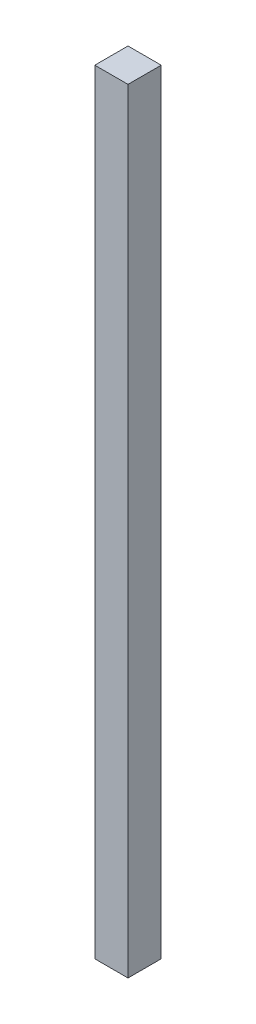
SolidWorks part; units mm, degrees
ref_plane "Plan de face" through (0, 0, 0) normal (0, 0, 1) x (1, 0, 0)
ref_plane "Plan de dessus" through (0, 0, 0) normal (0, 1, 0) x (1, 0, 0)
ref_plane "Plan de droite" through (0, 0, 0) normal (1, 0, 0) x (0, 0, -1)
sketch "Esquisse1" plane through (0, 0, 0) normal (0, 0, 1) x (1, 0, 0)
  line L1 (-41.6667, 69.6429) -> (-51.6667, 69.6429)
  line L2 (-41.6667, 69.6429) -> (-41.6667, -163.3571)
  line L3 (-41.6667, -163.3571) -> (-51.6667, -163.3571)
  line L4 (-51.6667, 69.6429) -> (-51.6667, -163.3571)
  dimension "D1" = 10
  dimension "D2" = 233
extrude "Boss.-Extru.1" add sketch "Esquisse1" along normal blind 10 contours L4 L3 L2 L1
equation "\"EpaisseurPlaque\"= 3"
equation "\"ProfondeurBoite\"=460"
equation "\"LongueurSyphon\"=270"
equation "\"LargeurSyphon\"=120"
equation "\"HauteurCoteDroit\"= 490"
equation "\"HauteurCoteGauche\"= 540"
equation "\"HauteurSolSyphon\"= 300"
equation "\"HauteurSyphon\"=\"HauteurCoteGauche\"-\"HauteurSolSyphon\""
equation "\"LargeurDroite\"=10"
equation "\"LargeurGauche\"=150"
equation "\"LargeurBoite\"= \"LargeurDroite\" + \"LargeurGauche\" + \"LargeurSyphon\""
equation "\"D2@Esquisse1\"=\"HauteurSyphon\" -7"
